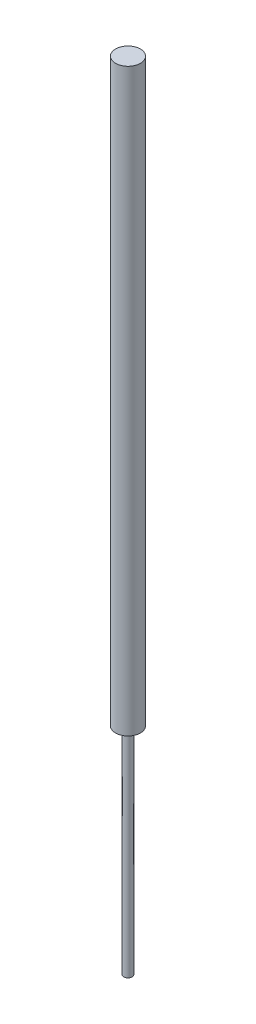
SolidWorks part; units mm, degrees
material "7075-T6 (SN)"
ref_plane "Front Plane" through (0, 0, 0) normal (0, 0, 1) x (1, 0, 0)
ref_plane "Top Plane" through (0, 0, 0) normal (0, 1, 0) x (1, 0, 0)
ref_plane "Right Plane" through (0, 0, 0) normal (1, 0, 0) x (0, 0, -1)
sketch "Sketch1" plane through (0, 0, 0) normal (0, 0, 1) x (1, 0, 0)
  line L0 (0, 0) -> (1.5875, 0)
  line L1 (1.5875, 0) -> (1.5875, 82.55)
  line L2 (1.5875, 82.55) -> (4.7625, 82.55)
  line L3 (4.7625, 82.55) -> (4.7625, 304.8)
  line L4 (4.7625, 304.8) -> (0, 304.8)
  line L5 (0, 304.8) -> (0, 0)
  dimension "D1" = 304.8
  dimension "D2" = 1.5875
  dimension "D3" = 4.7625
  dimension "D4" = 82.55
revolve "Revolve1" add sketch "Sketch1" angle 360 about L5
